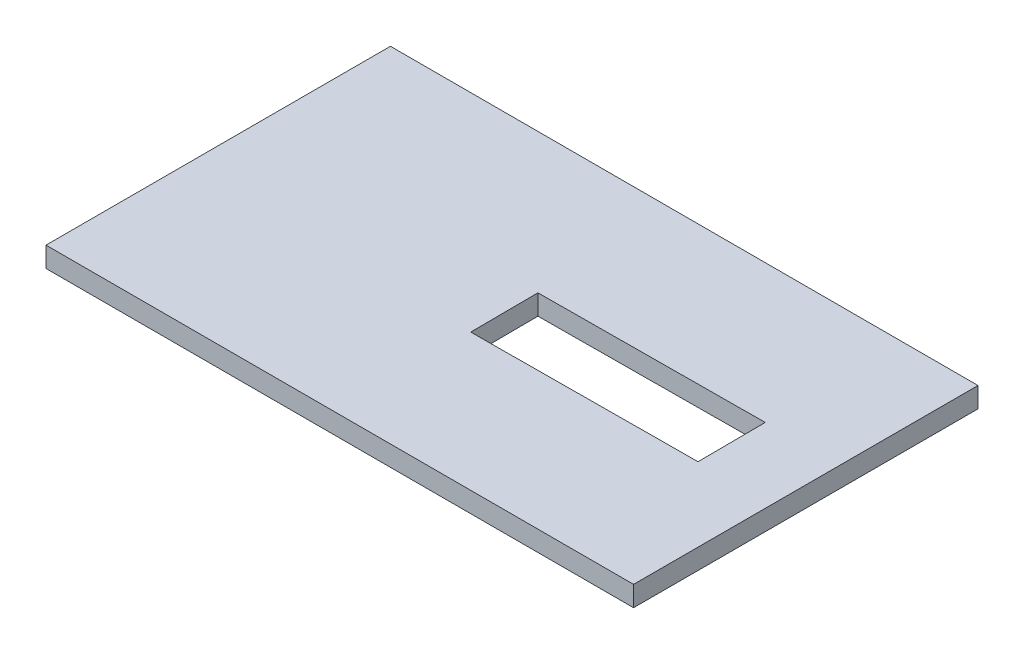
SolidWorks part; units mm, degrees
ref_plane "Спереди" through (0, 0, 0) normal (0, 0, 1) x (1, 0, 0)
ref_plane "Сверху" through (0, 0, 0) normal (0, 1, 0) x (1, 0, 0)
ref_plane "Справа" through (0, 0, 0) normal (1, 0, 0) x (0, 0, -1)
sketch "Эскиз1" plane through (0, 0, 0) normal (0, 1, 0) x (1, 0, 0)
  line L1 (0, 0) -> (5800, 0)
  line L2 (0, 0) -> (0, 3400)
  line L3 (0, 3400) -> (5800, 3400)
  line L4 (5800, 0) -> (5800, 3400)
extrude "Бобышка-Вытянуть1" add sketch "Эскиз1" along normal blind 200
sketch "Эскиз2" plane through (0, 200, 0) normal (0, 1, 0) x (1, 0, 0)
  line L1 (2835.6498, 2020.2788) -> (5065.6083, 2034.0493)
  line L2 (2835.6498, 2020.2788) -> (2839.771, 1352.9098)
  line L3 (2839.771, 1352.9098) -> (5069.7294, 1366.6803)
  line L4 (5065.6083, 2034.0493) -> (5069.7294, 1366.6803)
extrude "Вырез-Вытянуть1" cut sketch "Эскиз2" against normal blind 200
